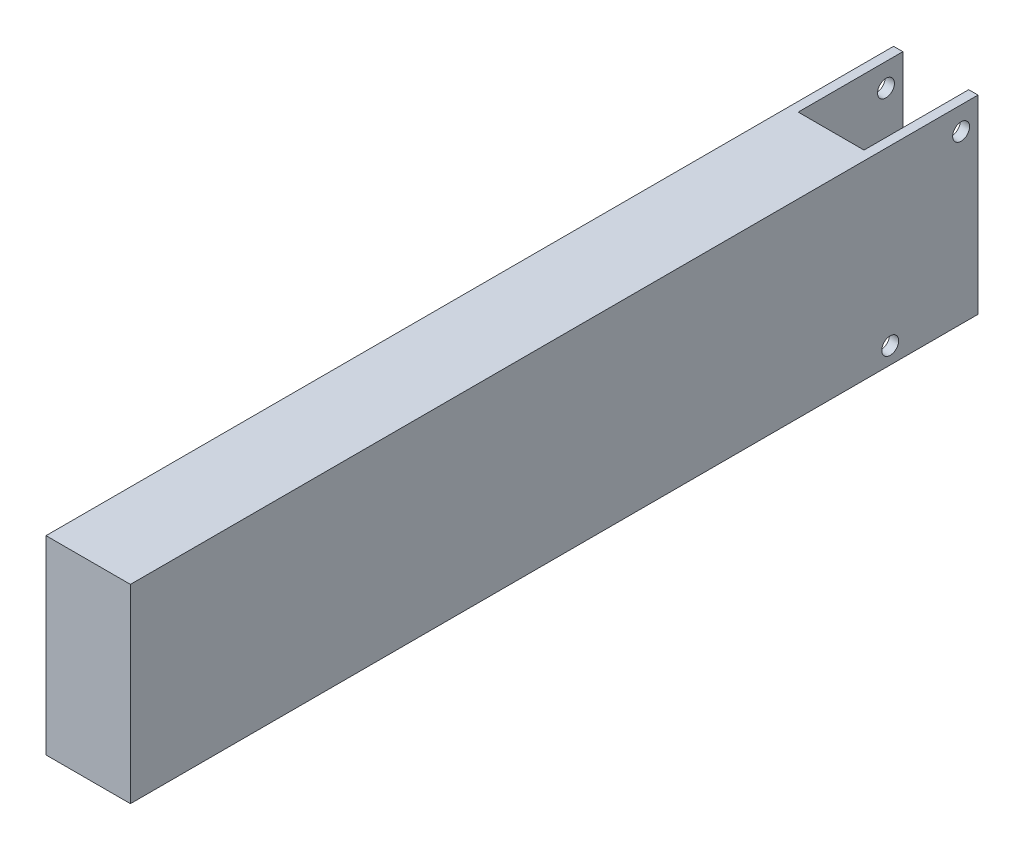
SolidWorks part; units mm, degrees
material "PVC 0.007 Plasticized"
ref_plane "Front Plane" through (0, 0, 0) normal (0, 0, 1) x (1, 0, 0)
ref_plane "Top Plane" through (0, 0, 0) normal (0, 1, 0) x (1, 0, 0)
ref_plane "Right Plane" through (0, 0, 0) normal (1, 0, 0) x (0, 0, -1)
sketch "Sketch1" plane through (0, 0, 0) normal (0, 0, 1) x (1, 0, 0)
  line L1 (0, 0) -> (12.7, 0)
  line L2 (0, 0) -> (0, 28.575)
  line L3 (0, 28.575) -> (12.7, 28.575)
  line L4 (12.7, 0) -> (12.7, 28.575)
  dimension "D1" = 12.7
  dimension "D2" = 28.575
extrude "Boss-Extrude1" add sketch "Sketch1" along normal blind 111.76
sketch "Sketch3" plane through (0, 0, 0) normal (0, 0, -1) x (-1, 0, 0)
  line L1 (-1.397, 28.575) -> (0, 28.575)
  line L2 (-1.397, 28.575) -> (-1.397, 0)
  line L3 (-1.397, 0) -> (0, 0)
  line L4 (0, 28.575) -> (0, 0)
  line L6 (0, 0) -> (-12.7, 0) construction
  line L8 (-12.7, 28.575) -> (-11.303, 28.575)
  line L9 (-12.7, 28.575) -> (-12.7, 0)
  line L10 (-12.7, 0) -> (-11.303, 0)
  line L11 (-11.303, 28.575) -> (-11.303, 0)
  dimension "D1" = 9.906
extrude "Boss-Extrude3" add sketch "Sketch3" along normal blind 15.748
sketch "Sketch7" plane through (0, 0, 0) normal (-1, 0, 0) x (0, 0, 1)
  line L0 (0, 0) -> (0, 28.575)
  line L1 (0, 0) -> (-15.748, 0)
  line L2 (-15.748, 0) -> (-15.748, 28.575)
  line L3 (0, 28.575) -> (-15.748, 28.575)
  circle A0 centre (-13.208, 25.0952) radius 1.27
  circle A1 centre (-2.54, 2.54) radius 1.27
  point P8 (0, 0)
  point P10 (-15.748, 28.575)
  dimension "D1" = 2.54
  dimension "D2" = 2.54
  dimension "D3" = 2.54
  dimension "D4" = 2.54
  dimension "D5" = 3.4798
  dimension "D6" = 2.54
  dimension "D7" = 15.748
  dimension "D8" = 28.575
extrude "Cut-Extrude3" cut sketch "Sketch7" against normal through all both contours A0 | A1
